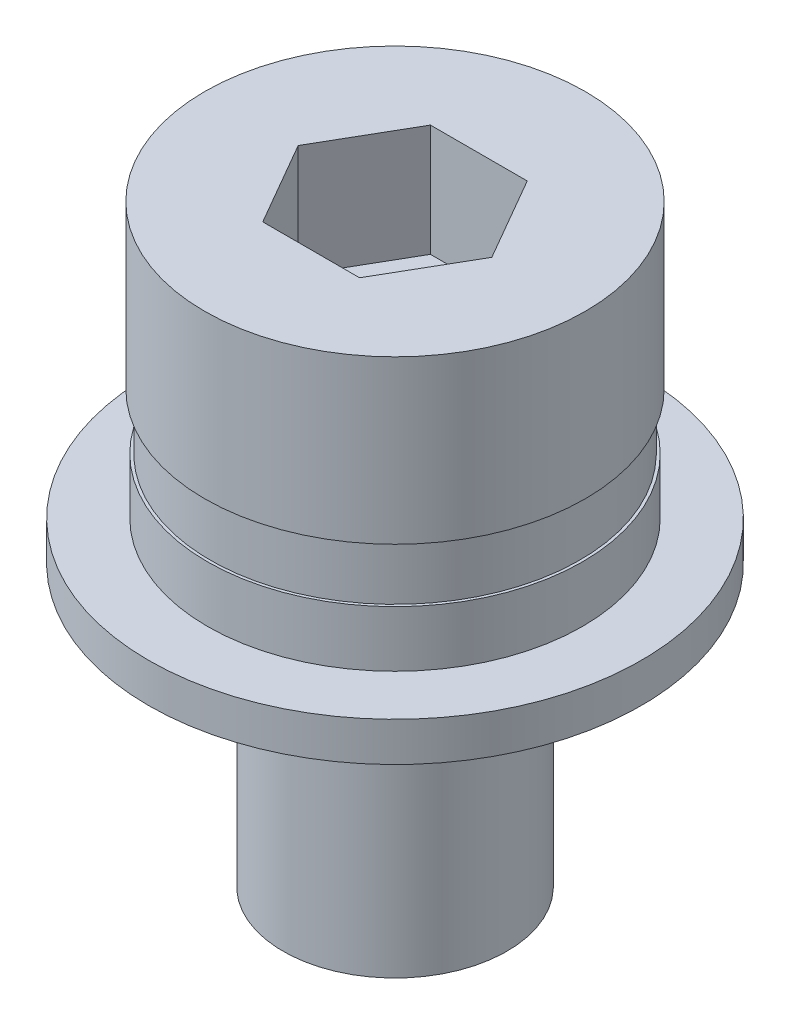
SolidWorks part; units mm, degrees
ref_plane "前视基准面" through (0, 0, 0) normal (0, 0, 1) x (1, 0, 0)
ref_plane "上视基准面" through (0, 0, 0) normal (0, 1, 0) x (1, 0, 0)
ref_plane "右视基准面" through (0, 0, 0) normal (1, 0, 0) x (0, 0, -1)
sketch "草图1" plane through (0, 0, 0) normal (0, 1, 0) x (1, 0, 0)
  circle A0 centre (0, 0) radius 4.4
  dimension "D1" = 8.8
extrude "凸台-拉伸1" add sketch "草图1" along normal blind 0.7
sketch "草图2" plane through (0, 0.7, 0) normal (0, 1, 0) x (1, 0, 0)
  circle A0 centre (0, 0) radius 3.35
  dimension "D1" = 6.7
extrude "凸台-拉伸2" add sketch "草图2" along normal blind 1
sketch "草图3" plane through (0, 1.7, 0) normal (0, 1, 0) x (1, 0, 0)
  circle A0 centre (0, 0) radius 3.4
  dimension "D1" = 6.8
extrude "凸台-拉伸3" add sketch "草图3" along normal blind 3.9
sketch "草图4" plane through (0, 1.7, 0) normal (0, -1, 0) x (1, 0, 0)
  circle A0 centre (0, 0) radius 3.3
  circle A1 centre (0, 0) radius 10.5263
  dimension "D1" = 6.6
extrude "切除-拉伸1" cut sketch "草图4" against normal blind 1
sketch "草图5" plane through (0, 5.6, 0) normal (0, 1, 0) x (1, 0, 0)
  line L1 (-1.7293, 0) -> (-0.8647, -1.4976)
  line L2 (-0.8647, -1.4976) -> (0.8647, -1.4976)
  line L3 (0.8647, -1.4976) -> (1.7293, 0)
  line L4 (1.7293, 0) -> (0.8647, 1.4976)
  line L5 (0.8647, 1.4976) -> (-0.8647, 1.4976)
  line L6 (-0.8647, 1.4976) -> (-1.7293, 0)
  circle A0 centre (0, 0) radius 1.4976 construction
extrude "切除-拉伸2" cut sketch "草图5" against normal blind 2
sketch "草图6" plane through (0, 0, 0) normal (0, -1, 0) x (1, 0, 0)
  circle A0 centre (0, 0) radius 2
  dimension "D1" = 4
extrude "凸台-拉伸4" add sketch "草图6" along normal blind 5
